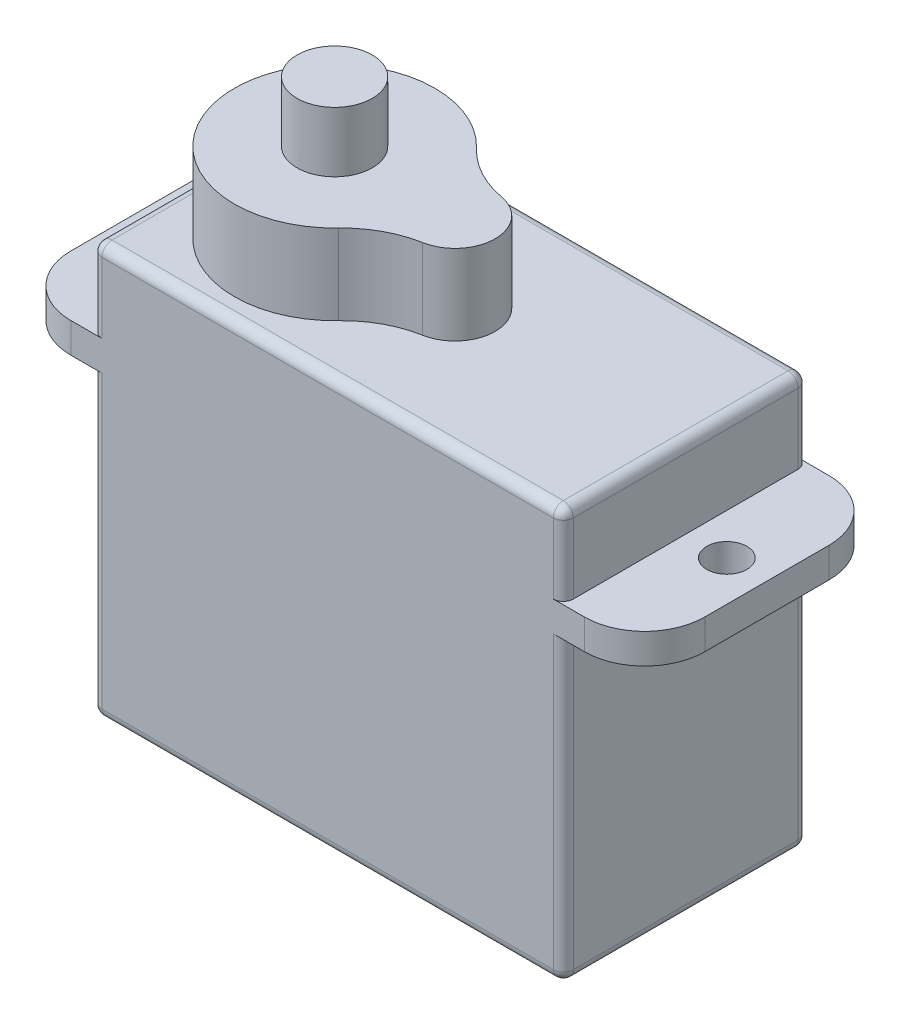
SolidWorks part; units mm, degrees
material "Alliage 1060"
ref_plane "Plan de face" through (0, 0, 0) normal (0, 0, 1) x (1, 0, 0)
ref_plane "Plan de dessus" through (0, 0, 0) normal (0, 1, 0) x (1, 0, 0)
ref_plane "Plan de droite" through (0, 0, 0) normal (1, 0, 0) x (0, 0, -1)
sketch "Esquisse1" plane through (0, 0, 0) normal (0, 0, 1) x (1, 0, 0)
  line L1 (-11.75, 0) -> (11.75, 0)
  line L2 (-11.75, 0) -> (-11.75, 20.5)
  line L3 (-11.75, 20.5) -> (11.75, 20.5)
  line L4 (11.75, 0) -> (11.75, 20.5)
  dimension "D1" = 23.5
  dimension "D2" = 20.5
extrude "corps" add sketch "Esquisse1" along normal mid plane 12.2
shell "Coque1" thickness 2
sketch "Esquisse2" plane through (0, 0, 0) normal (0, 1, 0) x (1, 0, 0)
  line L0 (0, 0) -> (-5.75, 0) construction
  line L1 (-11.75, -6.1) -> (-11.75, 6.1) construction
  arc A0 (-2.125, 3.4437) -> (-2.125, -3.4437) centre (-5.75, 0) ccw
  arc A1 (0.6071, -1.9679) -> (0.6071, 1.9679) centre (0.25, 0) ccw
  arc A2 (0.6071, 1.9679) -> (-2.125, 3.4437) centre (1.5, 6.8875) cw
  arc A3 (0.6071, -1.9679) -> (-2.125, -3.4437) centre (1.5, -6.8875) ccw
  dimension "D2" = 10
  dimension "D3" = 4
  dimension "D5" = 5
  dimension "D1" = 6
  dimension "D4" = 6
extrude "pivot_sortie" add sketch "Esquisse2" along normal blind 24.5
sketch "Esquisse3" plane through (0, 24.5, 0) normal (0, 1, 0) x (1, 0, 0)
  circle A0 centre (-5.75, 0) radius 1.875
  arc A1 (-2.125, 3.4437) -> (-2.125, -3.4437) centre (-5.75, 0) ccw construction
  dimension "D1" = 3.75
extrude "axe_sortie" add sketch "Esquisse3" along normal blind 3
ref_plane "Plan1" through (0, 15, 0) normal (0, -1, 0) x (1, 0, 0)
sketch "Esquisse4" plane through (0, 15, 0) normal (0, -1, 0) x (1, 0, 0)
  line L0 (11.75, -6.1) -> (-11.75, -6.1) construction
  line L1 (-15.8, 6.1) -> (15.8, 6.1)
  line L2 (-15.8, 6.1) -> (-15.8, -6.1)
  line L3 (-15.8, -6.1) -> (15.8, -6.1)
  line L4 (15.8, 6.1) -> (15.8, -6.1)
  line L5 (-15.8, 6.1) -> (15.8, -6.1) construction
  line L6 (-15.8, -6.1) -> (15.8, 6.1) construction
  line L7 (-13.8, 0) -> (13.8, 0) construction
  circle A0 centre (-13.8, 0) radius 1
  circle A1 centre (13.8, 0) radius 1
  point P0 (0, 0)
  dimension "D2" = 2
  dimension "D1" = 27.6
  dimension "D3" = 2
extrude "MIP_MAP" add sketch "Esquisse4" against normal blind 1.5
fillet "Congé1" radius 3 4 edges at (15.8, 15.75, 6.1) (15.8, 15.75, -6.1) (-15.8, 15.75, 6.1) (-15.8, 15.75, -6.1)
fillet "Congé2" radius 0.5 16 edges at (-11.75, 0, 0) (0, 0, 6.1) (11.75, 0, 0) (0, 0, -6.1) (-11.75, 7.5, -6.1) (-11.75, 7.5, 6.1) (-11.75, 18.5, -6.1) (-11.75, 18.5, 6.1) (-11.75, 20.5, 0) (0, 20.5, -6.1) (11.75, 20.5, 0) (0, 20.5, 6.1) (11.75, 7.5, -6.1) (11.75, 18.5, -6.1) (11.75, 18.5, 6.1) (11.75, 7.5, 6.1)
